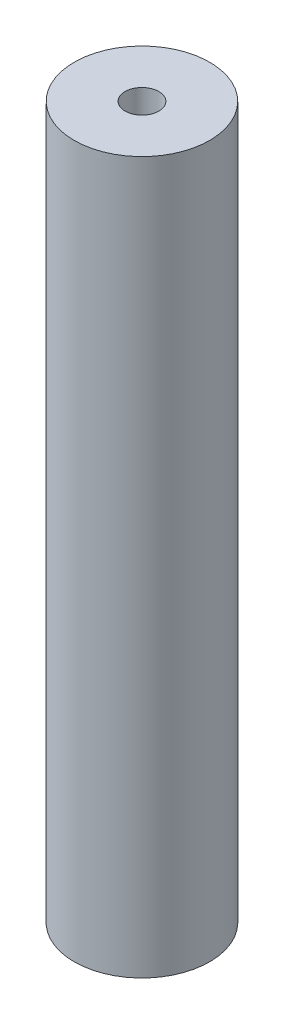
SolidWorks part; units mm, degrees
ref_plane "Front Plane" through (0, 0, 0) normal (0, 0, 1) x (1, 0, 0)
ref_plane "Top Plane" through (0, 0, 0) normal (0, 1, 0) x (1, 0, 0)
ref_plane "Right Plane" through (0, 0, 0) normal (1, 0, 0) x (0, 0, -1)
sketch "Sketch1" plane through (0, 0, 0) normal (0, 1, 0) x (1, 0, 0)
  circle A0 centre (0, 0) radius 10
  dimension "D1" = 20
extrude "Boss-Extrude1" add sketch "Sketch1" along normal blind 105
sketch "Sketch2" plane through (0, 105, 0) normal (0, 1, 0) x (1, 0, 0)
  circle A0 centre (0, 0) radius 2.5
  dimension "D1" = 5
extrude "Cut-Extrude1" cut sketch "Sketch2" against normal blind 8
sketch "Sketch3" plane through (0, 0, 0) normal (0, -1, 0) x (-1, 0, 0)
  circle A0 centre (0, 0) radius 2.5
  dimension "D1" = 5
extrude "Cut-Extrude2" cut sketch "Sketch3" against normal blind 8
